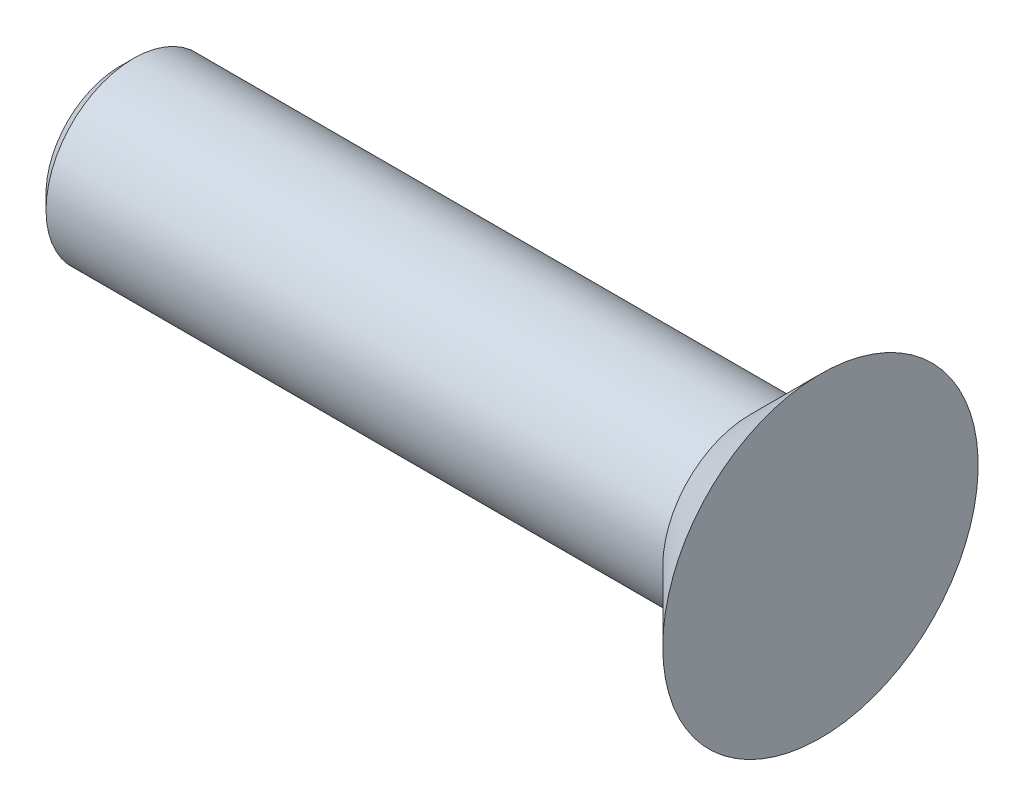
SolidWorks part; units mm, degrees
ref_plane "Plan de face" through (0, 0, 0) normal (0, 0, 1) x (1, 0, 0)
ref_plane "Plan de dessus" through (0, 0, 0) normal (0, 1, 0) x (1, 0, 0)
ref_plane "Plan de droite" through (0, 0, 0) normal (1, 0, 0) x (0, 0, -1)
sketch "Esquisse1" plane through (0, 0, 0) normal (0, 0, 1) x (1, 0, 0)
  line L0 (0, 0) -> (-20, 0)
  line L1 (-20, 0) -> (-20, 2.5)
  line L2 (-20, 2.5) -> (-2, 2.5)
  line L3 (-2, 2.5) -> (0, 4.5)
  line L4 (0, 4.5) -> (0, 0)
  line L5 (0, 0) -> (21.1509, 0) construction
  dimension "D1" = 45
  dimension "D2" = 2
  dimension "D3" = 5
  dimension "D4" = 20
revolve "Révolution1" add sketch "Esquisse1" angle 360 about L5
cosmetic thread "Représentation de filetage1" parameters "D2"=4.2
chamfer "Chanfrein1" distance 0.4 angle 45 1 edges at (-20, 0, 2.5)
